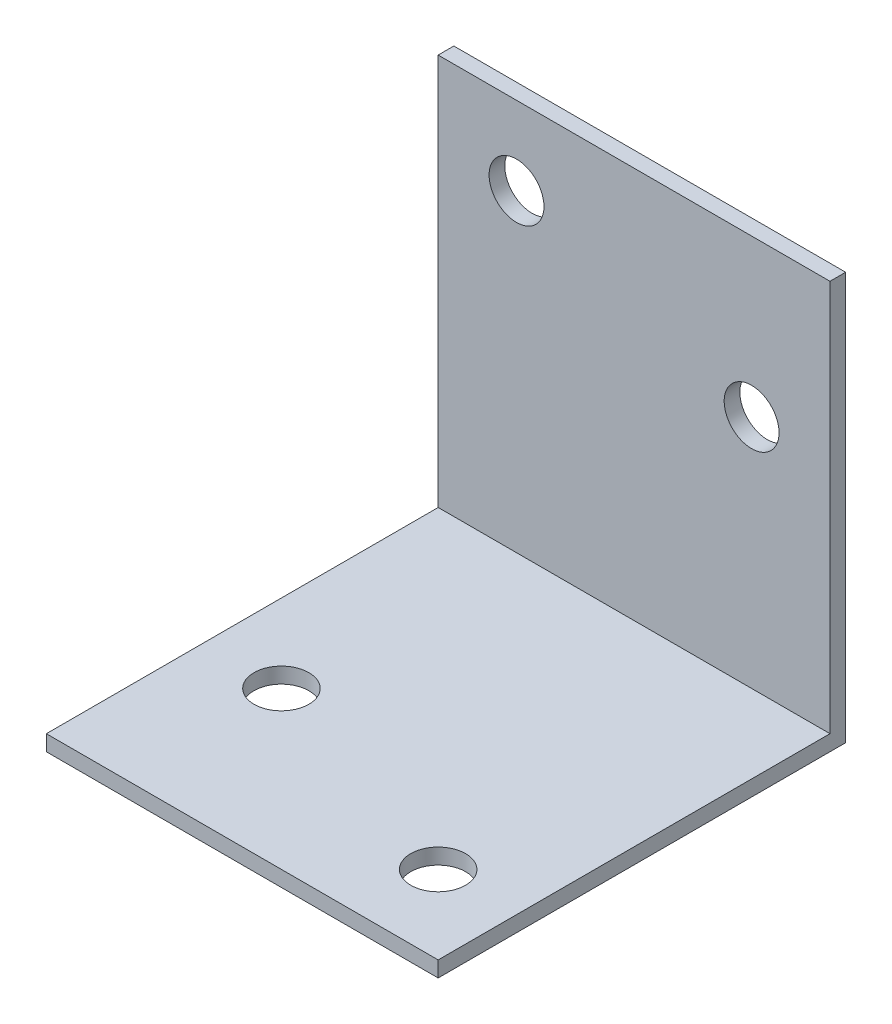
SolidWorks part; units mm, degrees
ref_plane "Front Plane" through (0, 0, 0) normal (0, 0, 1) x (1, 0, 0)
ref_plane "Top Plane" through (0, 0, 0) normal (0, 1, 0) x (1, 0, 0)
ref_plane "Right Plane" through (0, 0, 0) normal (1, 0, 0) x (0, 0, -1)
sketch "Sketch1" plane through (0, 0, 0) normal (0, 0, 1) x (1, 0, 0)
  line L1 (-12.5, 12.5) -> (12.5, 12.5)
  line L2 (-12.5, 12.5) -> (-12.5, -12.5)
  line L3 (-12.5, -12.5) -> (12.5, -12.5)
  line L4 (12.5, 12.5) -> (12.5, -12.5)
  line L5 (-12.5, 12.5) -> (12.5, -12.5) construction
  line L6 (-12.5, -12.5) -> (12.5, 12.5) construction
  circle A0 centre (7.5, 2.5) radius 1.75
  circle A1 centre (-7.5, 7.5) radius 1.75
  point P0 (0, 0)
  dimension "D5" = 3.5
  dimension "D1" = 25
  dimension "D2" = 25
  dimension "D3" = 10
  dimension "D4" = 5
  dimension "D6" = 5
  dimension "D7" = 5
extrude "Boss-Extrude2" add sketch "Sketch1" along normal blind 1
sketch "Sketch4" plane through (0, -12.5, 0) normal (0, -1, 0) x (1, 0, 0)
  line L1 (-12.5, 0) -> (12.5, 0)
  line L2 (-12.5, 0) -> (-12.5, 26)
  line L3 (-12.5, 26) -> (12.5, 26)
  line L4 (12.5, 0) -> (12.5, 26)
  circle A0 centre (7.5, 21) radius 1.75
  circle A1 centre (-7.5, 16) radius 1.75
  dimension "D5" = 3.5
  dimension "D1" = 25
  dimension "D2" = 26
  dimension "D3" = 5
  dimension "D4" = 5
  dimension "D6" = 10
  dimension "D7" = 5
extrude "Boss-Extrude3" add sketch "Sketch4" along normal blind 1
